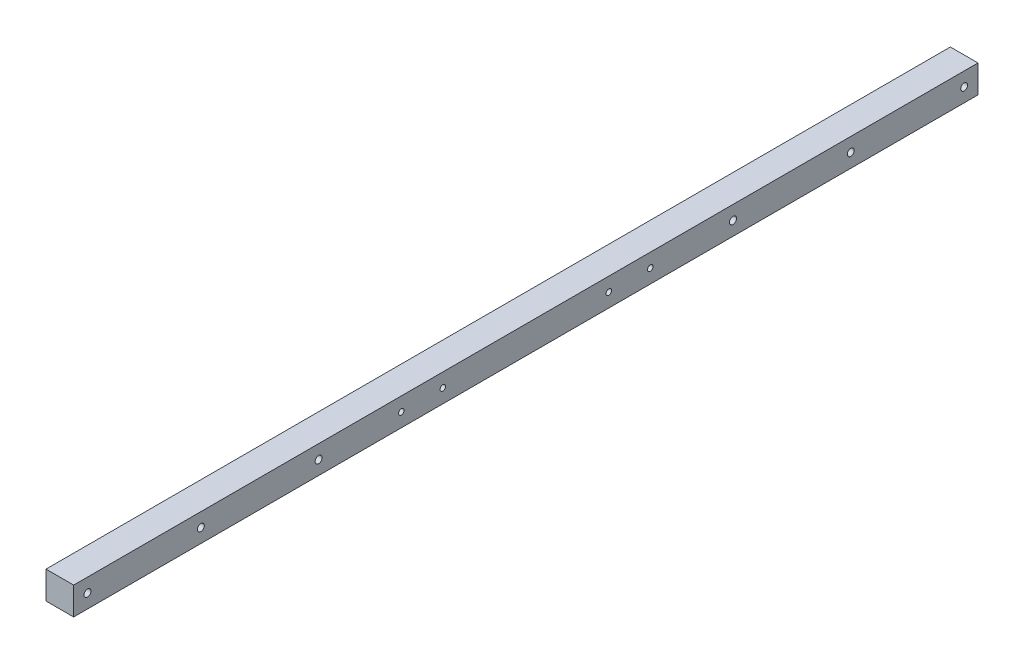
SolidWorks part; units mm, degrees
ref_plane "Front Plane" through (0, 0, 0) normal (0, 0, 1) x (1, 0, 0)
ref_plane "Top Plane" through (0, 0, 0) normal (0, 1, 0) x (1, 0, 0)
ref_plane "Right Plane" through (0, 0, 0) normal (1, 0, 0) x (0, 0, -1)
sketch "Sketch1" plane through (0, 0, 0) normal (0, 0, 1) x (1, 0, 0)
  line L5 (-12.7, -12.7) -> (12.7, -12.7)
  line L6 (-12.7, -12.7) -> (-12.7, 12.7)
  line L7 (-12.7, 12.7) -> (12.7, 12.7)
  line L8 (12.7, -12.7) -> (12.7, 12.7)
  line L9 (-12.7, -12.7) -> (12.7, 12.7) construction
  line L10 (-12.7, 12.7) -> (12.7, -12.7) construction
  point P0 (0, 0)
  dimension "D1" = 25.4
  dimension "D2" = 25.4
extrude "Boss-Extrude1" add sketch "Sketch1" along normal blind 830.58
sketch "Sketch2" plane through (-12.7, 0, 0) normal (1, 0, 0) x (0, 0, -1)
  line L0 (0, 0) -> (-830.58, 0) construction
  line L2 (0, 12.7) -> (0, -12.7) construction
  line L4 (0, -12.7) -> (0, 12.7) construction
  line L5 (-830.58, 12.7) -> (-830.58, -12.7) construction
  circle A0 centre (-12.7, 0) radius 3.175
  circle A2 centre (-116.84, 0) radius 3.175
  dimension "D1" = 6.35
  dimension "D2" = 12.7
  dimension "D3" = 104.14
ref_plane "Plane1" through (0, 0, 415.29) normal (0, 0, -1) x (-1, 0, 0)
extrude "Cut-Extrude4" cut sketch "Sketch2" along normal through all
mirror "Mirror1" about plane through (0, 0, 415.29) normal (0, 0, -1) of "Cut-Extrude4"
hole_wizard "1/4-20 Tapped Hole1" positions "Sketch4" profile "Sketch6" tap size "1/4-20" standard "ANSI Inch"
sketch "Sketch4" plane through (12.7, 0, 0) normal (1, 0, 0) x (0, 0, -1)
  line L2 (-300.99, 0) -> (-529.59, 0) construction
  line L4 (-415.29, 12.7) -> (-415.29, 0) construction
  line L6 (-830.58, 12.7) -> (0, 12.7) construction
  line L7 (-300.99, 0) -> (0, 0) construction
  line L8 (-491.49, 0) -> (-339.09, 0) construction
  point P0 (-300.99, 0)
  point P2 (-529.59, 0)
  point P27 (-491.49, 0)
  point P29 (-339.09, 0)
  point P37 (-415.29, 0)
  dimension "D1" = 228.6
  dimension "D2" = 152.4
sketch "Sketch6" plane through (12.7, 0, 300.99) normal (0, 1, 0) x (0, 0, -1)
  line L0 (0, 0) -> (0, 20.5838)
  line L1 (0, 20.5838) -> (2.5527, 19.05)
  line L2 (2.5527, 19.05) -> (2.5527, 0)
  line L5 (2.5527, 0) -> (0, 0)
  line L10 (0, 20.5838) -> (-2.5527, 19.05) construction
  line L11 (0, -6.35) -> (0, 107.95) construction
  dimension "Tap Drill Dia." = 5.1054
  dimension "Tap Drill Depth" = 19.05
  dimension "Drill Angle" = 118
cosmetic thread "Hole Thread1" parameters "D1"=17.78, "D2"=6.35
cosmetic thread "Hole Thread2" parameters "D1"=17.78, "D2"=6.35
cosmetic thread "Hole Thread3" parameters "D1"=17.78, "D2"=6.35
cosmetic thread "Hole Thread4" parameters "D1"=17.78, "D2"=6.35
sketch "Sketch7" plane through (-12.7, 0, 0) normal (-1, 0, 0) x (0, 0, 1)
  line L0 (830.58, 12.7) -> (830.58, -12.7) construction
  line L1 (0, 12.7) -> (0, -12.7) construction
  circle A0 centre (605.58, 0) radius 3.25
  circle A1 centre (225, 0) radius 3.25
  dimension "D1" = 6.5
  dimension "D3" = 6.5
  dimension "D2" = 225
  dimension "D4" = 225
extrude "Cut-Extrude5" cut sketch "Sketch7" against normal through all
